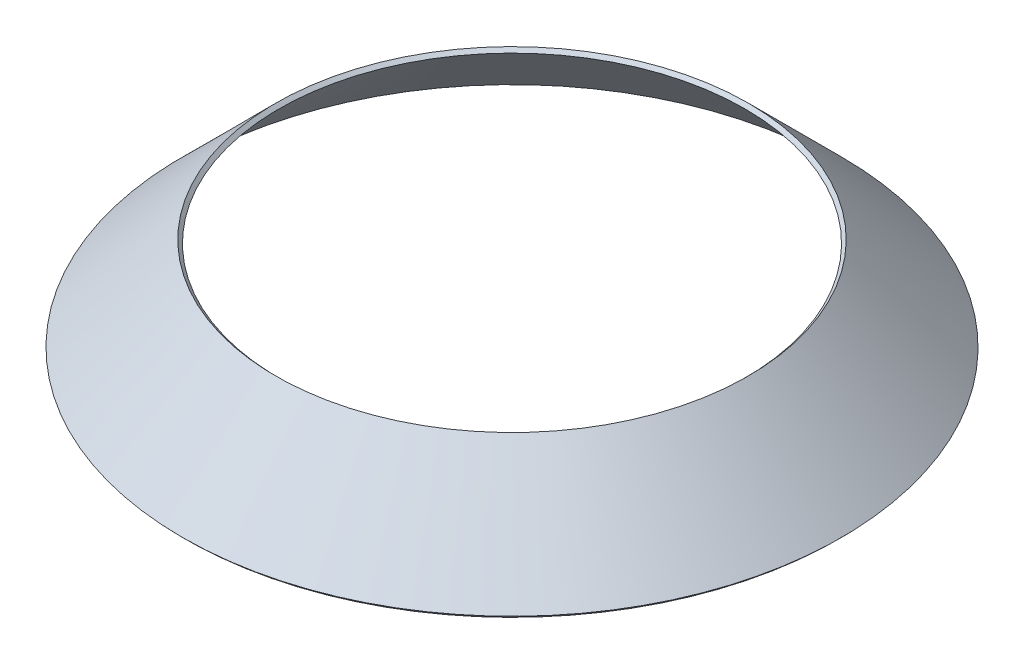
SolidWorks part; units mm, degrees
ref_plane "前视基准面" through (0, 0, 0) normal (0, 0, 1) x (1, 0, 0)
ref_plane "上视基准面" through (0, 0, 0) normal (0, 1, 0) x (1, 0, 0)
ref_plane "右视基准面" through (0, 0, 0) normal (1, 0, 0) x (0, 0, -1)
sketch "草图2" plane through (0, 0, 0) normal (1, 0, 0) x (0, 0, -1)
  line L0 (0, 0) -> (0, 0.8749) construction
sketch "草图1" plane through (0, 0, 0) normal (1, 0, 0) x (0, 0, -1)
  line L0 (5, 0.9867) -> (7, -1.0133)
  line L1 (5, 0.9867) -> (5.0707, 1.0574)
  line L2 (7, -1.0133) -> (7.0707, -0.9426)
  line L3 (5.0707, 1.0574) -> (7.0707, -0.9426)
  dimension "D1" = 5
  dimension "D2" = 7
  dimension "D3" = 2
  dimension "D4" = 0.1
revolve "旋转1" add sketch "草图1" angle 360 about L0
